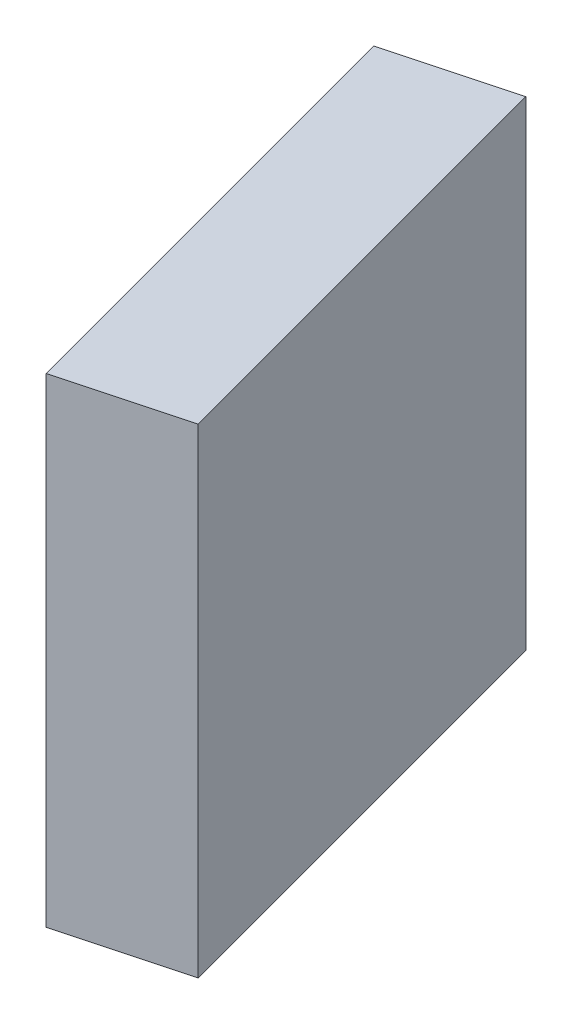
SolidWorks part; units mm, degrees
material "松木"
ref_plane "前视基准面" through (0, 0, 0) normal (0, 0, 1) x (1, 0, 0)
ref_plane "上视基准面" through (0, 0, 0) normal (0, 1, 0) x (1, 0, 0)
ref_plane "右视基准面" through (0, 0, 0) normal (1, 0, 0) x (0, 0, -1)
sketch "草图1" plane through (0, 0, 0) normal (0, 1, 0) x (1, 0, 0)
  line L0 (0, 0) -> (0, 50)
  line L1 (0, 50) -> (12.5, 3.3494)
  line L2 (12.5, 3.3494) -> (0, 0)
  line L3 (0, 50) -> (-12.5, 46.6506)
  line L4 (-12.5, 46.6506) -> (0, 0)
  dimension "D1" = 50
  dimension "D2" = 75
  dimension "D3" = 15
extrude "凸台-拉伸1" add sketch "草图1" along normal blind 50 contours L3 L4 L0 | L2 L1 L0
